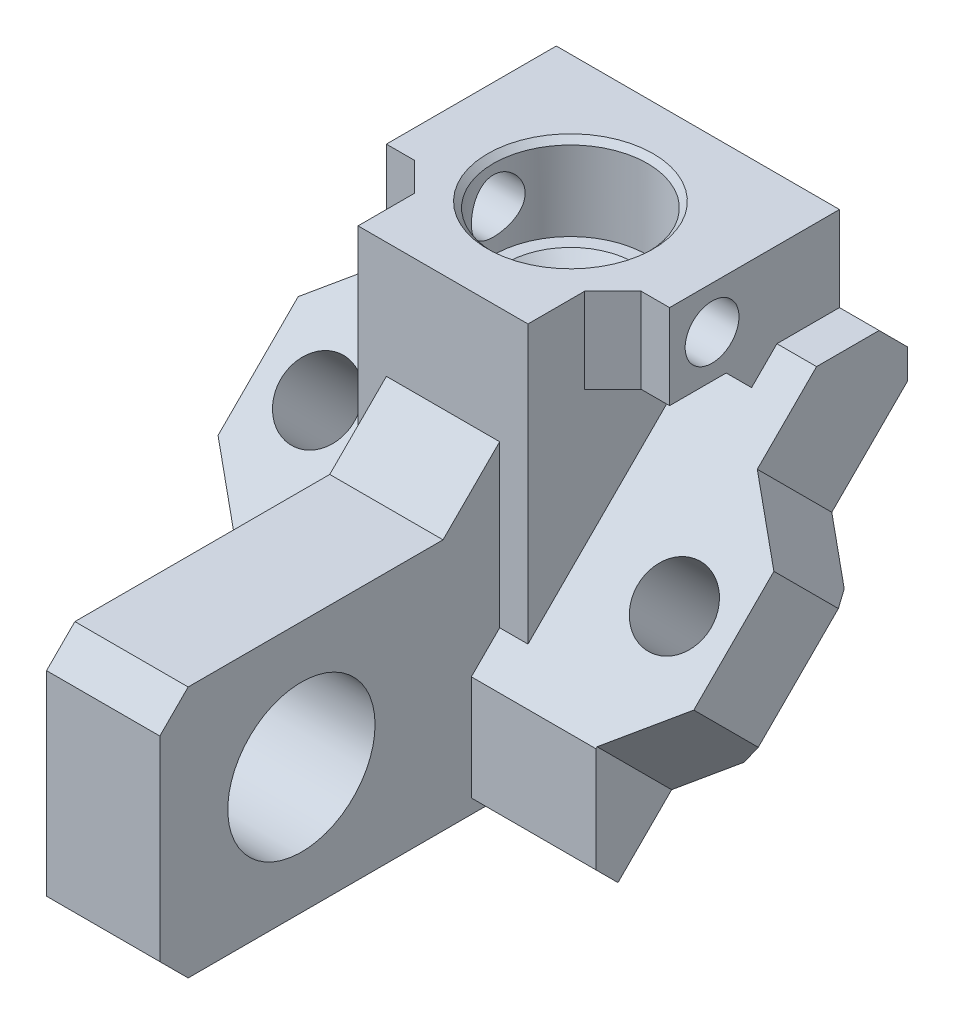
SolidWorks part; units mm, degrees
ref_plane "Front Plane" through (0, 0, 0) normal (0, 0, 1) x (1, 0, 0)
ref_plane "Top Plane" through (0, 0, 0) normal (0, 1, 0) x (1, 0, 0)
ref_plane "Right Plane" through (0, 0, 0) normal (1, 0, 0) x (0, 0, -1)
sketch "Sketch2" plane through (0, 0, 0) normal (1, 0, 0) x (0, 0, -1)
  line L1 (2.25, 0) -> (-2.25, 0)
  line L2 (2.25, 0) -> (2.25, 5.276)
  line L3 (2.25, 5.276) -> (-2.25, 5.276)
  line L4 (-2.25, 0) -> (-2.25, 5.276)
  dimension "D1" = 4.5
  dimension "D2" = 2.25
  dimension "D3" = 5.276
  dimension "D4" = 0
extrude "Boss-Extrude1" add sketch "Sketch2" along normal mid plane 3
sketch "Sketch3" plane through (0, 0, 0) normal (1, 0, 0) x (0, 0, -1)
  line L0 (0, 0) -> (2.75, 2.75)
  line L1 (2.75, 2.75) -> (2.75, 3.276)
  line L2 (2.75, 3.276) -> (2.25, 3.776)
  line L3 (2.25, 0) -> (2.25, 5.276) construction
  line L4 (2.25, 3.776) -> (1.1455, 3.776)
  line L5 (1.1455, 3.776) -> (-2.75, -0.1196)
  line L6 (-2.75, -0.1196) -> (-2.75, -1.9722)
  line L7 (-2.75, -1.9722) -> (-2.3611, -2.3611)
  line L8 (-2.3611, -2.3611) -> (0, 0)
  line L9 (-2.25, 0) -> (2.25, 0) construction
  line L11 (2.25, 5.276) -> (-2.25, 5.276) construction
  dimension "D1" = 180
  dimension "D2" = 5.5
  dimension "D3" = 45
  dimension "D4" = 1.86
  dimension "D5" = 0.5
  dimension "D6" = 0.55
  dimension "D7" = 1.5
extrude "Boss-Extrude2" add sketch "Sketch3" along normal mid plane 6.4
sketch "Sketch4" plane through (3.2, 0, 0) normal (1, 0, 0) x (0, 0, -1)
  line L0 (2.25, 2.25) -> (0, 0)
  line L1 (0, 0) -> (2.25, 0)
  line L2 (2.25, 0) -> (2.25, 2.25)
extrude "Cut-Extrude1" cut sketch "Sketch4" against normal through all
sketch "Sketch5" plane through (0, 0, 0) normal (1, 0, 0) x (0, 0, -1)
  line L0 (-2.4972, -2.225) -> (-7.75, -2.225)
  line L2 (-7.75, -2.225) -> (-8.25, -1.725)
  line L3 (-8.25, -1.725) -> (-8.25, 1.725)
  line L4 (-8.25, 1.725) -> (-7.75, 2.225)
  line L5 (-7.75, 2.225) -> (-3.25, 2.225)
  line L6 (-3.25, 2.225) -> (-2.25, 3.225)
  line L7 (-2.25, 5.276) -> (-2.25, 0.3804) construction
  line L8 (-2.25, 3.225) -> (-2.25, 0.3804)
  line L9 (-2.25, 0.3804) -> (-2.75, -0.1196)
  line L10 (-2.75, -0.1196) -> (-2.75, -1.9722)
  line L11 (-2.75, -1.9722) -> (-2.4972, -2.225)
  circle A0 centre (-5.75, 0) radius 1.3
  point P19 (-7.5574, 2.1913)
  dimension "D5" = 2.5
  dimension "D6" = 2.225
  dimension "D7" = 2.6
  dimension "D1" = 8.25
  dimension "D2" = 45
  dimension "D3" = 4.45
  dimension "D4" = 2.225
  dimension "D8" = 0.5
  dimension "D9" = 0.5
  dimension "D10" = 0.5
  dimension "D11" = 45
  dimension "D12" = 1
extrude "Boss-Extrude3" add sketch "Sketch5" along normal mid plane 2
sketch "Sketch6" plane through (0, 0, 0) normal (0, -0.7071, -0.7071) x (1, 0, 0)
  line L0 (-3.2, 2) -> (-4.2, 1)
  line L1 (-3.2, 3.3391) -> (-3.2, -3.8891) construction
  line L2 (-4.2, 1) -> (-4.2, -1)
  line L3 (-4.2, -1) -> (-3.2, -2)
  line L4 (-3.2, -2) -> (-3.2, 2)
  line L5 (0, 3.3391) -> (0, -4.261) construction
  line L8 (3.2, 3.3391) -> (-3.2, 3.3391) construction
  line L9 (1.5, -4.261) -> (-1.5, -4.261) construction
  line L10 (3.2, -2) -> (3.2, 2)
  line L11 (4.2, -1) -> (3.2, -2)
  line L12 (4.2, 1) -> (4.2, -1)
  line L13 (3.2, 2) -> (4.2, 1)
  dimension "D1" = 4.2
  dimension "D2" = 2
  dimension "D3" = 45
  dimension "D4" = 1
  dimension "D5" = 45
extrude "Boss-Extrude4" add sketch "Sketch6" against normal up to surface (1.86 mm away) up to face at (-1.9, 1.3456, 1.2848)
sketch "Sketch7" plane through (0, 0, 0) normal (0, -0.7071, -0.7071) x (1, 0, 0)
  circle A0 centre (-3.15, 0) radius 0.65
  circle A1 centre (3.15, 0) radius 0.65
  dimension "D3" = 1.3
  dimension "D4" = 1.3
  dimension "D1" = 6.3
  dimension "D2" = 3.15
extrude "Cut-Extrude2" cut sketch "Sketch7" against normal through all
sketch "Sketch8" plane through (0, 0, 0) normal (0, -0.7071, -0.7071) x (1, 0, 0)
  line L1 (-2.25, 2.84) -> (2.25, 2.84)
  line L2 (-2.25, 2.84) -> (-2.25, -2.5)
  line L3 (-2.25, -2.5) -> (2.25, -2.5)
  line L4 (2.25, 2.84) -> (2.25, -2.5)
  dimension "D1" = 4.5
  dimension "D2" = 5.34
  dimension "D3" = 2.5
  dimension "D4" = 2.25
extrude "Cut-Extrude3" cut sketch "Sketch8" against normal blind 0.7
fillet "Fillet1" radius 0.2 4 edges at (-2.25, 2.0153, -1.5203) (2.25, 2.0153, -1.5203) (2.25, -1.7607, 2.2557) (-2.25, -1.7607, 2.2557)
sketch "Sketch9" plane through (0, 0.495, 0.495) normal (0, -0.7071, -0.7071) x (1, 0, 0)
  line L0 (2.05, 2.84) -> (-2.05, 2.84) construction
  line L5 (-2.25, 2.84) -> (-1.06, 2.84)
  line L6 (-2.25, 2.84) -> (-2.25, 1.65)
  line L7 (-2.25, 1.65) -> (-1.06, 1.65)
  line L8 (-1.06, 2.84) -> (-1.06, 1.65)
  line L9 (-2.25, 2.64) -> (-2.25, -2.3) construction
  line L10 (0, 2.84) -> (0, -2.5) construction
  line L11 (2.05, 2.84) -> (-2.05, 2.84) construction
  line L12 (-2.05, -2.5) -> (2.05, -2.5) construction
  line L16 (1.06, 2.84) -> (1.06, 1.65)
  line L17 (2.25, 1.65) -> (1.06, 1.65)
  line L18 (2.25, 2.84) -> (2.25, 1.65)
  line L19 (2.25, 2.84) -> (1.06, 2.84)
  line L21 (2.25, -2.5) -> (1.06, -2.5)
  line L22 (2.25, -2.5) -> (2.25, -1.31)
  line L23 (2.25, -1.31) -> (1.06, -1.31)
  line L24 (1.06, -2.5) -> (1.06, -1.31)
  line L25 (-1.06, -2.5) -> (-1.06, -1.31)
  line L26 (-2.25, -1.31) -> (-1.06, -1.31)
  line L27 (-2.25, -2.5) -> (-2.25, -1.31)
  line L28 (-2.25, -2.5) -> (-1.06, -2.5)
  point P17 (2.25, 0.17)
  dimension "D1" = 1.19
  dimension "D2" = 1.19
  dimension "D3" = 0
  dimension "D4" = 0
extrude "Boss-Extrude5" add sketch "Sketch9" along normal blind 0.4
fillet "Fillet2" radius 0.5 4 edges at (-1.06, 1.2799, -0.5728) (1.06, 1.2799, -0.5728) (1.06, -0.8132, 1.5203) (-1.06, -0.8132, 1.5203)
sketch "Sketch11" plane through (0, 0, 0) normal (1, 0, 0) x (0, 0, -1)
  line L0 (2.25, 5.276) -> (-0.75, 5.276)
  line L1 (2.25, 5.276) -> (-2.25, 5.276) construction
  line L2 (-0.75, 5.276) -> (-0.75, 3.776)
  line L3 (-0.75, 3.776) -> (0.25, 3.776)
  line L4 (0.25, 3.776) -> (0.6978, 3.3282)
  line L5 (-2.25, 0.3804) -> (1.1455, 3.776) construction
  line L6 (0.6978, 3.3282) -> (1.1455, 3.776)
  line L7 (1.1455, 3.776) -> (2.25, 3.776)
  line L8 (2.25, 3.776) -> (2.25, 5.276)
  dimension "D1" = 1.5
  dimension "D2" = 1
  dimension "D3" = 3
extrude "Boss-Extrude6" add sketch "Sketch11" along normal mid plane 5
sketch "Sketch10" plane through (0, 5.276, 0) normal (0, 1, 0) x (1, 0, 0)
  circle A0 centre (0, 0) radius 0.925
  dimension "D1" = 1.85
extrude "Cut-Extrude4" cut sketch "Sketch10" against normal through all both and the other way through all
hole_wizard "M1.2x0.25 Tapped Hole1" positions "Sketch12" profile "Sketch13" tap size "M1.2x0.25" standard "ANSI Metric" end condition through all
sketch "Sketch12" plane through (2.5, 0, 0) normal (1, 0, 0) x (0, 0, -1)
  point P0 (0, 4.526)
sketch "Sketch13" plane through (2.5, 4.526, 0) normal (0, 1, 0) x (0, 0, -1)
  line L0 (0, 0) -> (0, 6.7)
  line L1 (0, 6.7) -> (0.475, 6.7)
  line L2 (0.475, 6.7) -> (0.475, 0)
  line L5 (0.475, 0) -> (0, 0)
  line L11 (0, -6.35) -> (0, 107.95) construction
  dimension "Thru Tap Drill Dia." = 0.95
  dimension "Thru Tap Drill Depth" = 6.7
cosmetic thread "Hole Thread1" parameters "D2"=1.2
chamfer "Chamfer1" distance 0.5 angle 45 2 edges at (-1.5, 4.526, 0.75) (1.5, 4.526, 0.75)
sketch "Sketch14" plane through (0, 5.276, 0) normal (0, 1, 0) x (1, 0, 0)
  circle A0 centre (0, 0) radius 1.36
  dimension "D1" = 2.72
extrude "Cut-Extrude5" cut sketch "Sketch14" against normal blind 1.5
chamfer "Chamfer2" distance 0.2 angle 45 1 edges at (0, 3.776, 0.925)
chamfer "Chamfer3" distance 0.1 angle 45 1 edges at (0, 5.276, 1.36)
chamfer "Chamfer4" distance 0.25 angle 45 2 edges at (-4.2, 0, 0) (4.2, 0, 0)
